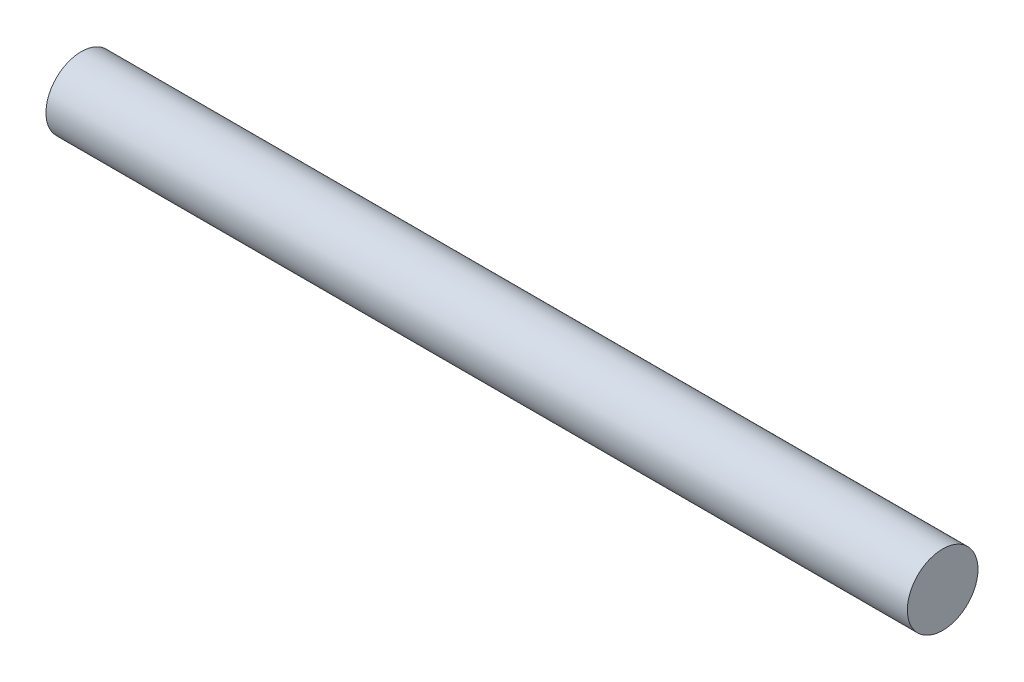
SolidWorks part; units mm, degrees
material "AISI 316 Annealed Stainless Steel Bar (SS)"
ref_plane "Front Plane" through (0, 0, 0) normal (0, 0, 1) x (1, 0, 0)
ref_plane "Top Plane" through (0, 0, 0) normal (0, 1, 0) x (1, 0, 0)
ref_plane "Right Plane" through (0, 0, 0) normal (1, 0, 0) x (0, 0, -1)
sketch "Sketch1" plane through (0, 0, 0) normal (1, 0, 0) x (0, 0, -1)
  circle A0 centre (0, 0) radius 4
  dimension "D1" = 8
extrude "Boss-Extrude1" add sketch "Sketch1" along normal blind 97.5
